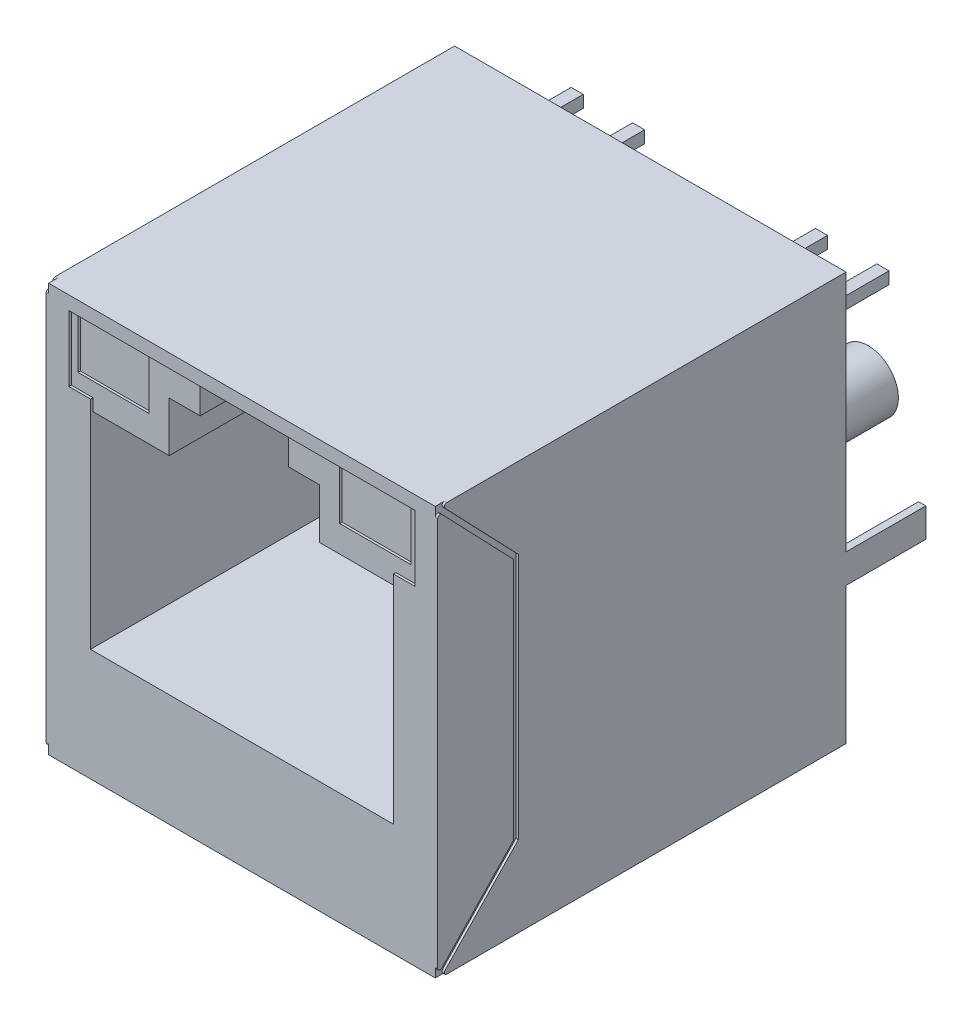
SolidWorks part; units mm, degrees
ref_plane "Спереди" through (0, 0, 0) normal (0, 0, 1) x (1, 0, 0)
ref_plane "Сверху" through (0, 0, 0) normal (0, 1, 0) x (1, 0, 0)
ref_plane "Справа" through (0, 0, 0) normal (1, 0, 0) x (0, 0, -1)
sketch "Эскиз1" plane through (0, 0, 0) normal (0, 0, 1) x (1, 0, 0)
  line L1 (-8.1, 8.45) -> (8.1, 8.45)
  line L2 (-8.1, 8.45) -> (-8.1, -8.45)
  line L3 (-8.1, -8.45) -> (8.1, -8.45)
  line L4 (8.1, 8.45) -> (8.1, -8.45)
  line L5 (-8.1, 8.45) -> (8.1, -8.45) construction
  line L6 (-8.1, -8.45) -> (8.1, 8.45) construction
  point P0 (0, 0)
  dimension "D1" = 16.2
  dimension "D2" = 16.9
extrude "Бобышка-Вытянуть1" add sketch "Эскиз1" along normal blind 16.9
sketch "Эскиз2" plane through (0, 0, 16.9) normal (0, 0, 1) x (1, 0, 0)
  line L0 (35.4424, 121.9932) -> (210.7757, 121.9932) construction
  line L1 (-6.2649, -3.8039) -> (-6.2649, 4.6644)
  line L2 (-6.2649, 4.6644) -> (-3.1078, 4.6644)
  line L3 (-3.1078, 4.6644) -> (-3.1078, 6.7309)
  line L4 (-3.1078, 6.7309) -> (-1.829, 6.7309)
  line L5 (-1.829, 6.7309) -> (-1.829, 7.8902)
  line L6 (0, 0) -> (0, 10.8636) construction
  line L7 (1.829, 6.7309) -> (1.829, 7.8902)
  line L8 (3.1078, 6.7309) -> (1.829, 6.7309)
  line L9 (3.1078, 4.6644) -> (3.1078, 6.7309)
  line L10 (6.2649, 4.6644) -> (3.1078, 4.6644)
  line L11 (6.2649, -3.8039) -> (6.2649, 4.6644)
  line L12 (-1.829, 7.8902) -> (1.829, 7.8902)
  line L13 (-6.2649, -3.8039) -> (6.2649, -3.8039)
extrude "Вырез-Вытянуть1" cut sketch "Эскиз2" against normal blind 10
sketch "Эскиз3" plane through (0, 0, 16.9) normal (0, 0, 1) x (1, 0, 0)
  line L0 (0, 0) -> (0, 10.8636) construction
  line L1 (-6.8884, 7.8204) -> (-3.9421, 7.8204)
  line L2 (-6.8884, 7.8204) -> (-6.8884, 5.7601)
  line L3 (-6.8884, 5.7601) -> (-3.9421, 5.7601)
  line L4 (-3.9421, 7.8204) -> (-3.9421, 5.7601)
  line L5 (6.8884, 5.7601) -> (3.9421, 5.7601)
  line L6 (3.9421, 7.8204) -> (3.9421, 5.7601)
  line L7 (6.8884, 7.8204) -> (3.9421, 7.8204)
  line L8 (6.8884, 7.8204) -> (6.8884, 5.7601)
extrude "Вырез-Вытянуть2" cut sketch "Эскиз3" against normal blind 0.2
sketch "Эскиз4" plane through (0, 0, 16.9) normal (0, 0, 1) x (1, 0, 0)
  line L0 (0, 0) -> (0, 10.8636) construction
  line L1 (-7.1617, 5.1649) -> (7.1617, 5.1649)
  line L2 (-7.1617, 5.1649) -> (-7.1617, 7.8902)
  line L3 (-7.1617, 7.8902) -> (7.1617, 7.8902)
  line L4 (7.1617, 5.1649) -> (7.1617, 7.8902)
extrude "Вырез-Вытянуть3" cut sketch "Эскиз4" against normal blind 0.1
sketch "Эскиз5" plane through (0, 0, 16.9) normal (0, 0, 1) x (1, 0, 0)
  line L0 (3.1078, 5.1649) -> (7.1617, 5.1649) construction
  line L1 (-6.2649, 4.6644) -> (6.2649, 4.6644)
  line L2 (-6.2649, 4.6644) -> (-6.2649, 5.1649)
  line L3 (-6.2649, 5.1649) -> (6.2649, 5.1649)
  line L4 (6.2649, 4.6644) -> (6.2649, 5.1649)
extrude "Вырез-Вытянуть4" cut sketch "Эскиз5" against normal blind 0.1
chamfer "Фаска1" distance 0.5 angle 45 12 edges at (-6.2649, 0.4302, 6.9) (-4.6864, 4.6644, 6.9) (-3.1078, 5.6976, 6.9) (-2.4684, 6.7309, 6.9) (-1.829, 7.3106, 6.9) (0, 7.8902, 6.9) (1.829, 7.3106, 6.9) (2.4684, 6.7309, 6.9) (3.1078, 5.6976, 6.9) (4.6864, 4.6644, 6.9) (6.2649, 0.4302, 6.9) (0, -3.8039, 6.9)
sketch "Эскиз6" plane through (-8.1, 0, 0) normal (-1, 0, 0) x (0, 0, 1)
  line L0 (16.7585, 8.45) -> (13.562, 5.1151)
  line L1 (16.9, 8.45) -> (0, 8.45) construction
  line L2 (13.562, 5.1151) -> (13.562, -5.1151)
  line L3 (13.562, -5.1151) -> (16.7585, -8.45)
  line L4 (16.9, -8.45) -> (0, -8.45) construction
  line L5 (0, 0) -> (16.9, 0) construction
  line L6 (0, 8.45) -> (0, -8.45) construction
  line L7 (16.9, 8.45) -> (16.9, -8.45) construction
  line L8 (16.7585, 8.45) -> (16.9, 8.45)
  line L9 (16.9, 8.45) -> (16.9, 8.3085)
  line L10 (16.9, 8.3085) -> (13.7661, 5.0391)
  line L11 (13.7661, 5.0391) -> (13.7661, -5.0391)
  line L12 (16.9, -8.3085) -> (13.7661, -5.0391)
  line L13 (16.9, -8.45) -> (16.9, -8.3085)
  line L14 (16.7585, -8.45) -> (16.9, -8.45)
  line L15 (15.1603, 6.7826) -> (15.3331, 6.6738) construction
  line L16 (13.7661, 5.0391) -> (13.562, 5.0391) construction
  point P20 (13.7661, 0)
  dimension "D1" = 0.2
extrude "Вырез-Вытянуть5" cut sketch "Эскиз6" against normal blind 0.1
mirror "Зеркальное отражение1" about plane through (0, 0, 0) normal (1, 0, 0) of "Вырез-Вытянуть5"
fillet "Скругление1" radius 0.1 8 edges at (8.05, -8.45, 16.7585) (8.05, -8.3085, 16.9) (-8.05, -8.45, 16.7585) (-8.05, -8.3085, 16.9) (8.05, 8.3085, 16.9) (8.05, 8.45, 16.7585) (-8.05, 8.45, 16.7585) (-8.05, 8.3085, 16.9)
sketch "Эскиз7" plane through (0, 0, 0) normal (0, 0, -1) x (-1, 0, 0)
  line L0 (45.3642, 146.8294) -> (260.6975, 146.8294) construction
  line L1 (8.1, -8.45) -> (-8.1, -8.45) construction
  line L2 (-4.7424, -4.83) -> (-4.2424, -4.83)
  line L3 (-4.7424, -4.83) -> (-4.7424, -4.43)
  line L4 (-4.7424, -4.43) -> (-4.2424, -4.43)
  line L5 (-4.2424, -4.83) -> (-4.2424, -4.43)
  line L6 (-4.7424, -4.83) -> (-4.2424, -4.43) construction
  line L7 (-4.7424, -4.43) -> (-4.2424, -4.83) construction
  line L8 (-3.4724, -7.37) -> (-2.9724, -7.37)
  line L9 (-3.4724, -7.37) -> (-3.4724, -6.97)
  line L10 (-3.4724, -6.97) -> (-2.9724, -6.97)
  line L11 (-2.9724, -7.37) -> (-2.9724, -6.97)
  line L12 (-3.4724, -7.37) -> (-2.9724, -6.97) construction
  line L13 (-3.4724, -6.97) -> (-2.9724, -7.37) construction
  line L14 (-2.2024, -4.83) -> (-2.2024, -4.43)
  line L15 (-2.2024, -4.83) -> (-1.7024, -4.83)
  line L16 (-1.7024, -4.83) -> (-1.7024, -4.43)
  line L17 (-2.2024, -4.43) -> (-1.7024, -4.43)
  line L18 (-0.9324, -7.37) -> (-0.9324, -6.97)
  line L19 (-0.9324, -7.37) -> (-0.4324, -7.37)
  line L20 (-0.4324, -7.37) -> (-0.4324, -6.97)
  line L21 (-0.9324, -6.97) -> (-0.4324, -6.97)
  line L22 (0.3376, -4.83) -> (0.3376, -4.43)
  line L23 (0.3376, -4.83) -> (0.8376, -4.83)
  line L24 (0.8376, -4.83) -> (0.8376, -4.43)
  line L25 (0.3376, -4.43) -> (0.8376, -4.43)
  line L26 (1.6076, -7.37) -> (1.6076, -6.97)
  line L27 (1.6076, -7.37) -> (2.1076, -7.37)
  line L28 (2.1076, -7.37) -> (2.1076, -6.97)
  line L29 (1.6076, -6.97) -> (2.1076, -6.97)
  line L30 (2.8776, -4.83) -> (2.8776, -4.43)
  line L31 (2.8776, -4.83) -> (3.3776, -4.83)
  line L32 (3.3776, -4.83) -> (3.3776, -4.43)
  line L33 (2.8776, -4.43) -> (3.3776, -4.43)
  line L34 (4.1476, -7.37) -> (4.1476, -6.97)
  line L35 (4.1476, -7.37) -> (4.6476, -7.37)
  line L36 (4.6476, -7.37) -> (4.6476, -6.97)
  line L37 (4.1476, -6.97) -> (4.6476, -6.97)
  line L38 (0, 0) -> (0, -8.45) construction
  line L39 (-6.575, 6.08) -> (-6.075, 6.08)
  line L40 (-6.575, 6.08) -> (-6.575, 5.58)
  line L41 (-6.575, 5.58) -> (-6.075, 5.58)
  line L42 (-6.075, 6.08) -> (-6.075, 5.58)
  line L43 (-6.575, 6.08) -> (-6.075, 5.58) construction
  line L44 (-6.575, 5.58) -> (-6.075, 6.08) construction
  line L45 (-4.035, 6.08) -> (-3.535, 6.08)
  line L46 (-4.035, 6.08) -> (-4.035, 5.58)
  line L47 (-4.035, 5.58) -> (-3.535, 5.58)
  line L48 (-3.535, 6.08) -> (-3.535, 5.58)
  line L49 (-4.035, 6.08) -> (-3.535, 5.58) construction
  line L50 (-4.035, 5.58) -> (-3.535, 6.08) construction
  line L51 (4.035, 5.58) -> (3.535, 5.58)
  line L52 (3.535, 6.08) -> (3.535, 5.58)
  line L53 (4.035, 6.08) -> (3.535, 6.08)
  line L54 (4.035, 6.08) -> (4.035, 5.58)
  line L55 (6.575, 5.58) -> (6.075, 5.58)
  line L56 (6.075, 6.08) -> (6.075, 5.58)
  line L57 (6.575, 6.08) -> (6.075, 6.08)
  line L58 (6.575, 6.08) -> (6.575, 5.58)
  line L59 (0, 0) -> (0, 8.45) construction
  line L60 (-8.1, 8.45) -> (8.1, 8.45) construction
  line L61 (-8.1, -8.45) -> (-8.1, 8.45) construction
  line L62 (-8.1, -1.58) -> (-7.8, -1.58)
  line L63 (-8.1, -1.58) -> (-8.1, -2.78)
  line L64 (-8.1, -2.78) -> (-7.8, -2.78)
  line L65 (-7.8, -1.58) -> (-7.8, -2.78)
  line L66 (-8.1, -1.58) -> (-7.8, -2.78) construction
  line L67 (-8.1, -2.78) -> (-7.8, -1.58) construction
  line L68 (8.1, -2.78) -> (7.8, -2.78)
  line L69 (7.8, -1.58) -> (7.8, -2.78)
  line L70 (8.1, -1.58) -> (7.8, -1.58)
  line L71 (8.1, -1.58) -> (8.1, -2.78)
  circle A0 centre (-5.715, 1.72) radius 1.25
  circle A1 centre (5.715, 1.72) radius 1.25
  point P2 (-4.4924, -4.63)
  point P7 (-3.2224, -7.17)
  point P15 (-6.325, 5.83)
  point P43 (-3.785, 5.83)
  point P59 (-7.95, -2.18)
  point P69 (-8.1, -1.1548)
  point P72 (0, 0)
  dimension "D15" = 2.5
  dimension "D1" = 0.5
  dimension "D2" = 0.4
  dimension "D3" = 2.54
  dimension "D4" = 1.27
  dimension "D5" = 6.73
  dimension "D7" = 3.785
  dimension "D8" = 6.325
  dimension "D9" = 13
  dimension "D10" = 15.9
  dimension "D11" = 5.715
  dimension "D12" = 8.89
  dimension "D13" = 3.9
  dimension "D14" = 1.2
  dimension "D16" = 0.5
  dimension "D6" = 4
extrude "Бобышка-Вытянуть2" add sketch "Эскиз7" along normal blind 3.3
sketch "Эскиз8" plane through (0, 0, 0) normal (0, 1, 0) x (1, 0, 0)
  line L0 (0, 0) -> (0, 10.6713) construction
